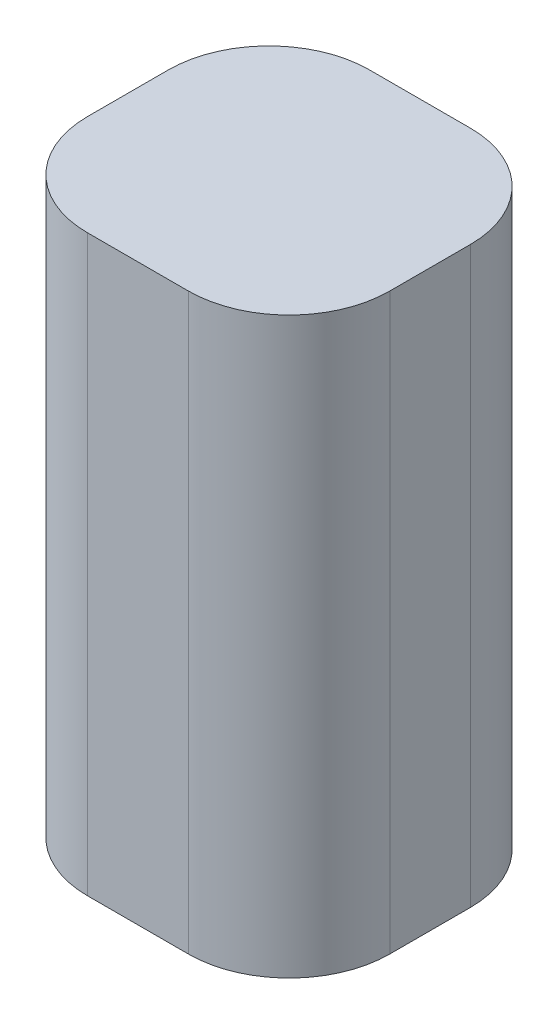
SolidWorks part; units mm, degrees
ref_plane "Front" through (0, 0, 0) normal (0, 0, 1) x (1, 0, 0)
ref_plane "Top" through (0, 0, 0) normal (0, 1, 0) x (1, 0, 0)
ref_plane "Right" through (0, 0, 0) normal (1, 0, 0) x (0, 0, -1)
sketch "Sketch1" plane through (0, 0, 0) normal (0, 0, 1) x (1, 0, 0)
  line L1 (-15, -28.5) -> (15, -28.5)
  line L2 (-15, -28.5) -> (-15, 28.5)
  line L3 (-15, 28.5) -> (15, 28.5)
  line L4 (15, -28.5) -> (15, 28.5)
  line L5 (-15, -28.5) -> (15, 28.5) construction
  line L6 (-15, 28.5) -> (15, -28.5) construction
  point P0 (0, 0)
  dimension "D1" = 57
  dimension "D2" = 30
extrude "Boss-Extrude1" add sketch "Sketch1" along normal blind 28
fillet "Fillet1" radius 10 4 edges at (-15, 0, 0) (15, 0, 0) (-15, 0, 28) (15, 0, 28)
